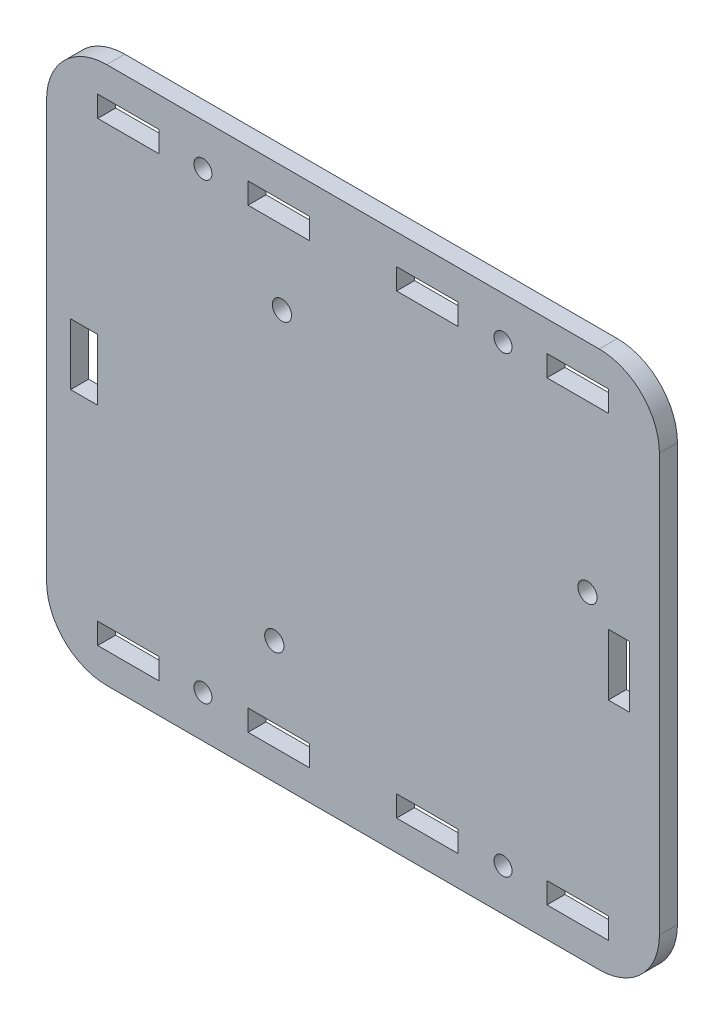
SolidWorks part; units mm, degrees
ref_plane "Front Plane" through (0, 0, 0) normal (0, 0, 1) x (1, 0, 0)
ref_plane "Top Plane" through (0, 0, 0) normal (0, 1, 0) x (1, 0, 0)
ref_plane "Right Plane" through (0, 0, 0) normal (1, 0, 0) x (0, 0, -1)
sketch "Model" plane through (0, 0, 0) normal (0, 0, 1) x (1, 0, 0)
  line L0 (54.7, -77.4) -> (54.7, -80.9)
  line L1 (54.7, -80.9) -> (64.9, -80.9)
  line L2 (64.9, -80.9) -> (64.9, -77.4)
  line L3 (64.9, -77.4) -> (54.7, -77.4)
  line L4 (5, -80.9) -> (15.2, -80.9)
  line L5 (15.2, -80.9) -> (15.2, -77.4)
  line L6 (15.2, -77.4) -> (5, -77.4)
  line L7 (5, -77.4) -> (5, -80.9)
  line L8 (54.7, -5) -> (64.9, -5)
  line L9 (64.9, -5) -> (64.9, -1.5)
  line L10 (64.9, -1.5) -> (54.7, -1.5)
  line L11 (54.7, -1.5) -> (54.7, -5)
  line L12 (5, -5) -> (15.2, -5)
  line L13 (15.2, -5) -> (15.2, -1.5)
  line L14 (15.2, -1.5) -> (5, -1.5)
  line L15 (5, -1.5) -> (5, -5)
  line L16 (0.5, -46.3) -> (5, -46.3)
  line L17 (5, -46.3) -> (5, -36.1)
  line L18 (5, -36.1) -> (0.5, -36.1)
  line L19 (0.5, -36.1) -> (0.5, -46.3)
  line L20 (6.5, -85.9) -> (88.4, -85.9)
  line L21 (-3.5, -6.5) -> (-3.5, -75.9)
  line L22 (6.5, 3.5) -> (88.4, 3.5)
  line L23 (98.4, -6.5) -> (98.4, -75.9)
  line L24 (89.9, -36.1) -> (89.9, -46.3)
  line L25 (89.9, -46.3) -> (93.4, -46.3)
  line L26 (93.4, -46.3) -> (93.4, -36.1)
  line L27 (93.4, -36.1) -> (89.9, -36.1)
  line L28 (30, -1.5) -> (30, -5)
  line L29 (30, -5) -> (40.2, -5)
  line L30 (40.2, -5) -> (40.2, -1.5)
  line L31 (40.2, -1.5) -> (30, -1.5)
  line L32 (79.7, -1.5) -> (79.7, -5)
  line L33 (79.7, -5) -> (89.9, -5)
  line L34 (89.9, -5) -> (89.9, -1.5)
  line L35 (89.9, -1.5) -> (79.7, -1.5)
  line L36 (30, -77.4) -> (30, -80.9)
  line L37 (30, -80.9) -> (40.2, -80.9)
  line L38 (40.2, -80.9) -> (40.2, -77.4)
  line L39 (40.2, -77.4) -> (30, -77.4)
  line L40 (79.7, -77.4) -> (79.7, -80.9)
  line L41 (79.7, -80.9) -> (89.9, -80.9)
  line L42 (89.9, -80.9) -> (89.9, -77.4)
  line L43 (89.9, -77.4) -> (79.7, -77.4)
  circle A0 centre (35.64, -17.27) radius 1.6
  circle A1 centre (34.37, -65.53) radius 1.6
  circle A2 centre (22.5, -78.9) radius 1.5
  circle A3 centre (72.4, -3.5) radius 1.5
  circle A4 centre (22.5, -3.5) radius 1.5
  circle A5 centre (72.4, -78.9) radius 1.5
  circle A6 centre (86.44, -32.51) radius 1.6
  arc A7 (6.5, 3.5) -> (-3.5, -6.5) centre (6.5, -6.5) ccw
  arc A8 (98.4, -75.9) -> (88.4, -85.9) centre (88.4, -75.9) cw
  arc A9 (-3.5, -75.9) -> (6.5, -85.9) centre (6.5, -75.9) ccw
  arc A10 (88.4, 3.5) -> (98.4, -6.5) centre (88.4, -6.5) cw
  dimension "D4" = 5
  dimension "D7" = 10
  dimension "D8" = 10
  dimension "D1" = 84.9
  dimension "D2" = 72.4
  dimension "D3" = 4
  dimension "D5" = 5
  dimension "D6" = 5
  dimension "D9" = 4.5
extrude "Boss-Extrude1" add sketch "Model" along normal blind 3
